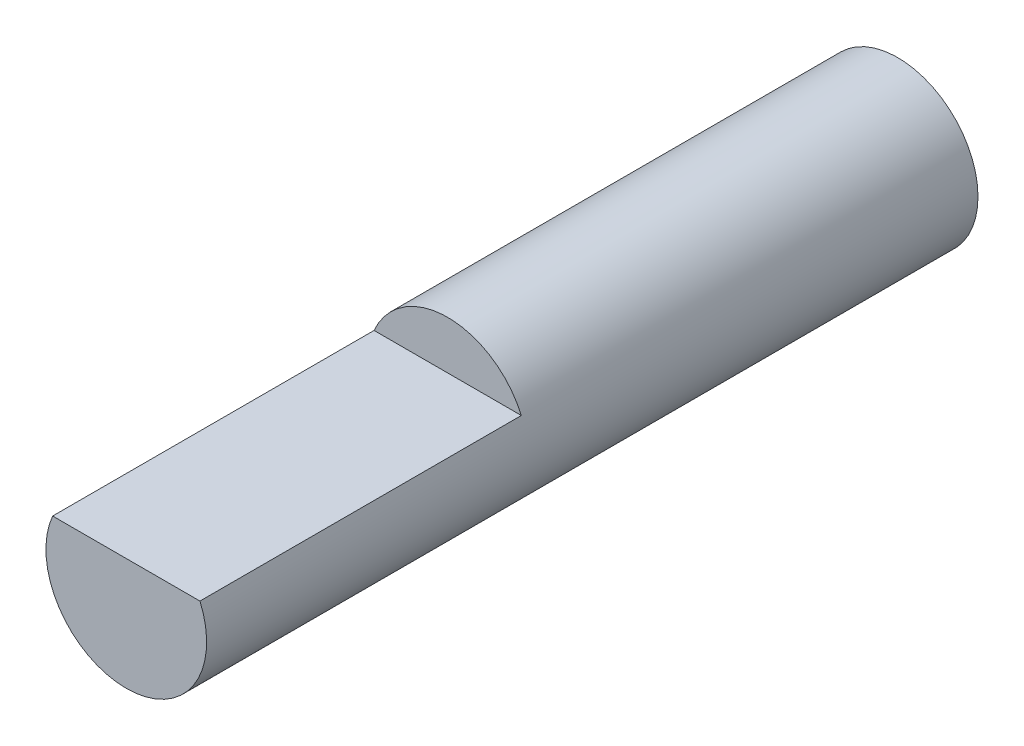
SolidWorks part; units mm, degrees
ref_plane "Alzado" through (0, 0, 0) normal (0, 0, 1) x (1, 0, 0)
ref_plane "Planta" through (0, 0, 0) normal (0, 1, 0) x (1, 0, 0)
ref_plane "Vista lateral" through (0, 0, 0) normal (1, 0, 0) x (0, 0, -1)
sketch "Croquis2" plane through (0, 0, 0) normal (0, 0, 1) x (1, 0, 0)
  circle A0 centre (0, 0) radius 2.5
  dimension "D1" = 5
extrude "Saliente-Extruir1" add sketch "Croquis2" along normal blind 24 contours A0
sketch "Croquis3" plane through (0, 0, 24) normal (0, 0, 1) x (1, 0, 0)
  line L0 (0, 0) -> (0, 1) construction
  line L1 (-2.2913, 1) -> (2.2913, 1)
  circle A0 centre (0, 0) radius 2.5 construction
  arc A1 (2.2913, 1) -> (-2.2913, 1) centre (0, 0) ccw
extrude "Cortar-Extruir1" cut sketch "Croquis3" against normal blind 10
